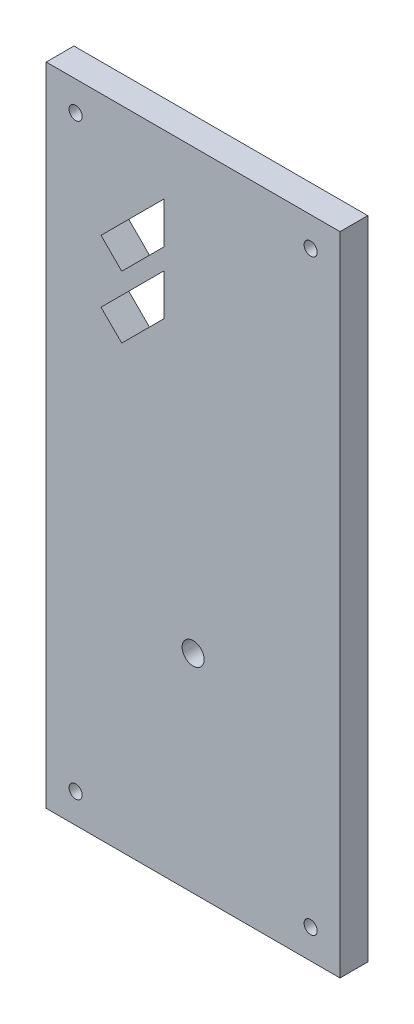
SolidWorks part; units mm, degrees
ref_plane "Front Plane" through (0, 0, 0) normal (0, 0, 1) x (1, 0, 0)
ref_plane "Top Plane" through (0, 0, 0) normal (0, 1, 0) x (1, 0, 0)
ref_plane "Right Plane" through (0, 0, 0) normal (1, 0, 0) x (0, 0, -1)
sketch "Sketch1" plane through (0, 0, 0) normal (0, 0, 1) x (1, 0, 0)
  line L0 (31.75, 139.7) -> (31.75, 0) construction
  line L1 (0, 0) -> (63.5, 0)
  line L2 (0, 0) -> (0, 139.7)
  line L3 (0, 139.7) -> (63.5, 139.7)
  line L4 (63.5, 0) -> (63.5, 139.7)
  line L5 (63.5, 69.85) -> (0, 69.85) construction
  line L6 (25.4818, 104.4111) -> (25.4818, 113.3691)
  line L7 (25.4818, 113.3691) -> (11.8417, 99.729)
  line L8 (11.8417, 99.729) -> (16.3207, 95.25)
  line L9 (16.3207, 95.25) -> (25.4818, 104.4111)
  line L10 (25.4818, 117.8592) -> (25.4818, 126.8171)
  line L11 (25.4818, 126.8171) -> (11.8417, 113.177)
  line L12 (11.8417, 113.177) -> (16.3207, 108.6981)
  line L13 (16.3207, 108.6981) -> (25.4818, 117.8592)
  circle A0 centre (6.35, 133.35) radius 1.4224
  circle A1 centre (57.15, 133.35) radius 1.4224
  circle A2 centre (57.15, 6.35) radius 1.4224
  circle A3 centre (6.35, 6.35) radius 1.4224
  circle A4 centre (31.75, 44.8945) radius 2.3812
  dimension "D3" = 2.8448
  dimension "D4" = 50.8
  dimension "D5" = 127
  dimension "D10" = 4.7625
  dimension "D1" = 63.5
  dimension "D2" = 139.7
  dimension "D6" = 25.4
  dimension "D7" = 63.5
  dimension "D8" = 44.8945
  dimension "D11" = 45
  dimension "D12" = 6.3342
  dimension "D13" = 9.1611
  dimension "D14" = 25.4
  dimension "D15" = 3.175
extrude "Boss-Extrude1" add sketch "Sketch1" along normal blind 5.9944
